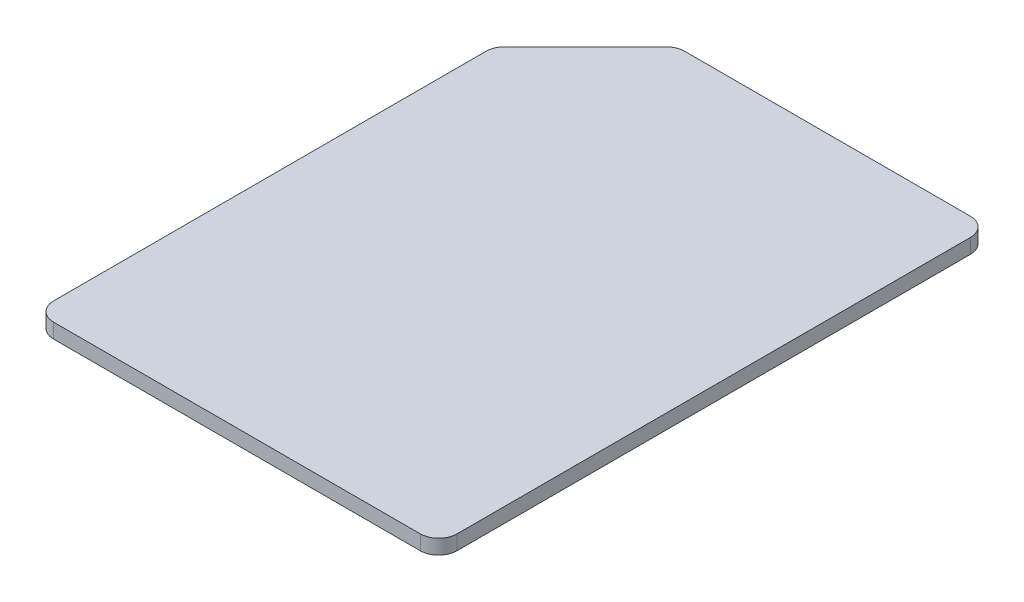
SolidWorks part; units mm, degrees
ref_plane "Front Plane" through (0, 0, 0) normal (0, 0, 1) x (1, 0, 0)
ref_plane "Top Plane" through (0, 0, 0) normal (0, 1, 0) x (1, 0, 0)
ref_plane "Right Plane" through (0, 0, 0) normal (1, 0, 0) x (0, 0, -1)
sketch "Sketch1" plane through (0, 0, 0) normal (0, 1, 0) x (1, 0, 0)
  line L1 (-5.5, -7.5) -> (5.5, -7.5)
  line L2 (-5.5, -7.5) -> (-5.5, 7.5)
  line L3 (-5.5, 7.5) -> (5.5, 7.5)
  line L4 (5.5, -7.5) -> (5.5, 7.5)
  line L5 (-5.5, -7.5) -> (5.5, 7.5) construction
  line L6 (-5.5, 7.5) -> (5.5, -7.5) construction
  point P0 (0, 0)
  dimension "D1" = 11
  dimension "D2" = 15
extrude "Boss-Extrude1" add sketch "Sketch1" along normal blind 0.4
chamfer "Chamfer1" distance 2.5 angle 45 1 edges at (-5.5, 0.2, -7.5)
fillet "Fillet1" radius 0.5 5 edges at (5.5, 0.2, 7.5) (-5.5, 0.2, 7.5) (5.5, 0.2, -7.5) (-3, 0.2, -7.5) (-5.5, 0.2, -5)
